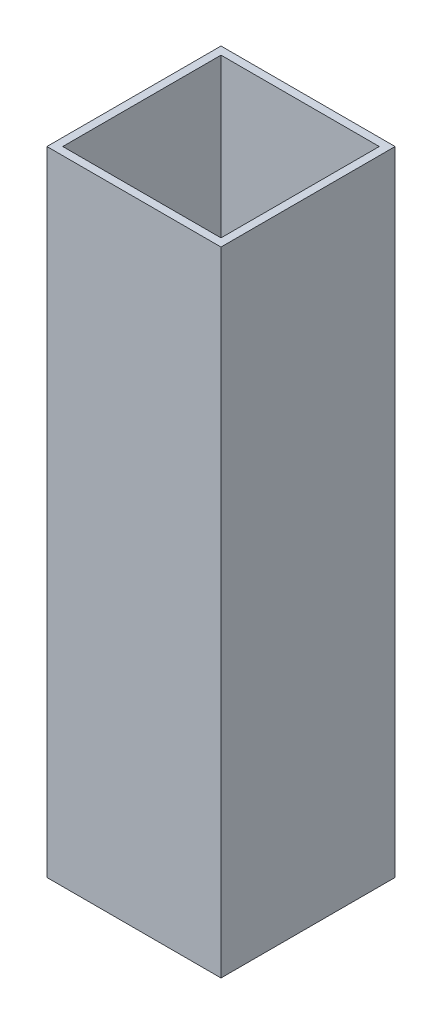
SolidWorks part; units mm, degrees
ref_plane "Front Plane" through (0, 0, 0) normal (0, 0, 1) x (1, 0, 0)
ref_plane "Top Plane" through (0, 0, 0) normal (0, 1, 0) x (1, 0, 0)
ref_plane "Right Plane" through (0, 0, 0) normal (1, 0, 0) x (0, 0, -1)
sketch "Sketch1" plane through (0, 0, 0) normal (0, 1, 0) x (1, 0, 0)
  line L1 (-10.6405, 10.5144) -> (0.3595, 10.5144)
  line L2 (-10.6405, 10.5144) -> (-10.6405, -0.4856)
  line L3 (-10.6405, -0.4856) -> (0.3595, -0.4856)
  line L4 (0.3595, 10.5144) -> (0.3595, -0.4856)
  dimension "D1" = 11
  dimension "D2" = 11
extrude "Boss-Extrude2" add sketch "Sketch1" along normal blind 40
shell "Shell1" thickness 0.5
